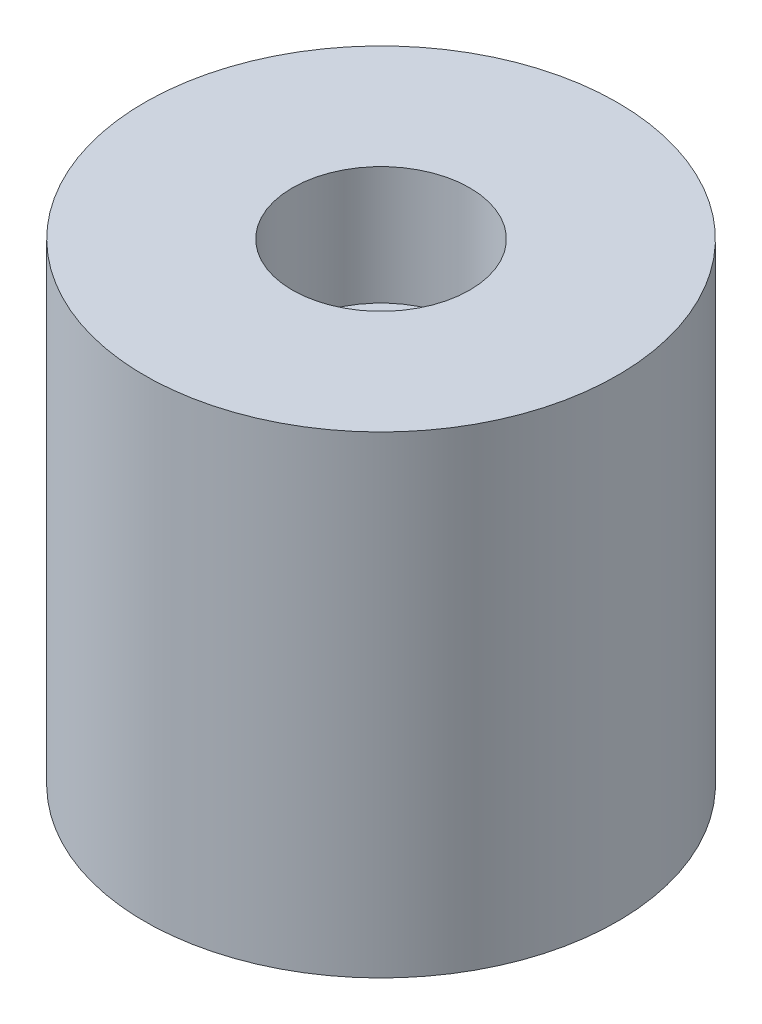
SolidWorks part; units mm, degrees
ref_plane "Front Plane" through (0, 0, 0) normal (0, 0, 1) x (1, 0, 0)
ref_plane "Top Plane" through (0, 0, 0) normal (0, 1, 0) x (1, 0, 0)
ref_plane "Right Plane" through (0, 0, 0) normal (1, 0, 0) x (0, 0, -1)
sketch "Sketch2" plane through (0, 0, 0) normal (0, 0, 1) x (1, 0, 0)
  line L0 (0, 0) -> (0, 9.525) construction
  line L1 (1.9844, -12.7) -> (12.7, -12.7)
  line L2 (1.9844, -12.7) -> (1.9844, 12.7)
  line L3 (1.9844, 12.7) -> (12.7, 12.7)
  line L4 (12.7, -12.7) -> (12.7, 12.7)
  line L6 (1.9844, 12.7) -> (4.7625, 12.7)
  line L7 (1.9844, 12.7) -> (1.9844, 6.35)
  line L8 (1.9844, 6.35) -> (4.7625, 6.35)
  line L9 (4.7625, 12.7) -> (4.7625, 6.35)
  point P8 (1.9844, 0)
  dimension "D1" = 12.7
  dimension "D2" = 1.9844
  dimension "D3" = 25.4
  dimension "D4" = 4.7625
  dimension "D5" = 19.05
revolve "Revolve1" add sketch "Sketch2" angle 360 about L0
